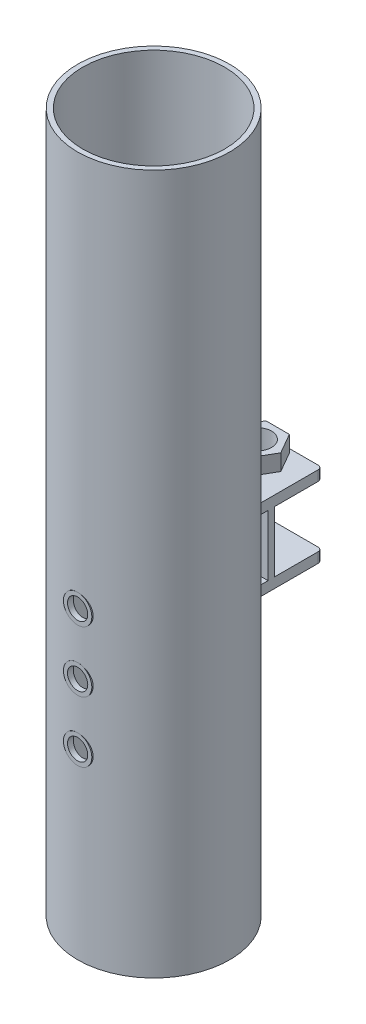
SolidWorks part; units mm, degrees
material "ASTM A36 Steel"
ref_plane "Front Plane" through (0, 0, 0) normal (0, 0, 1) x (1, 0, 0)
ref_plane "Top Plane" through (0, 0, 0) normal (0, 1, 0) x (1, 0, 0)
ref_plane "Right Plane" through (0, 0, 0) normal (1, 0, 0) x (0, 0, -1)
sketch "Sketch1" plane through (0, 0, 0) normal (0, 1, 0) x (1, 0, 0)
  circle A0 centre (0, 0) radius 35
  circle A1 centre (0, 0) radius 37.5
  dimension "D1" = 75
  dimension "D2" = 70
extrude "Boss-Extrude1" add sketch "Sketch1" along normal blind 345
sketch "Sketch2" plane through (0, 0, 0) normal (0, -1, 0) x (1, 0, 0)
  circle A0 centre (0, 0) radius 33.5
  circle A1 centre (0, 0) radius 35.5
  dimension "D1" = 2
extrude "Cut-Extrude1" cut sketch "Sketch2" against normal blind 20
ref_plane "Plane1" through (0, 0, 36.5) normal (0, 0, 1) x (1, 0, 0)
sketch "Sketch3" plane through (0, 0, 36.5) normal (0, 0, 1) x (1, 0, 0)
  line L0 (0, 0) -> (0, 20)
  circle A0 centre (0, 120) radius 5
  circle A1 centre (0, 90) radius 5
  circle A2 centre (0, 150) radius 5
extrude "Cut-Extrude2" cut sketch "Sketch3" against normal blind 30 and the other way blind 10
sketch "Sketch5" plane through (0, 0, 36.5) normal (0, 0, 1) x (1, 0, 0)
  circle A4 centre (0, 120) radius 7
  circle A5 centre (0, 90) radius 7
  circle A6 centre (0, 90) radius 5
  circle A7 centre (0, 120) radius 5
extrude "Boss-Extrude3" add sketch "Sketch5" against normal blind 1 separate body
sketch "Sketch6" plane through (0, 0, 36.5) normal (0, 0, 1) x (1, 0, 0)
  line L0 (0, 90) -> (0, 120)
  line L1 (0, 120) -> (0, 150)
  circle A1 centre (0, 120) radius 7
  circle A4 centre (0, 150) radius 7
  circle A5 centre (0, 120) radius 5
  circle A6 centre (0, 150) radius 5
  circle A8 centre (0, 90) radius 5
  circle A9 centre (0, 90) radius 7
extrude "Boss-Extrude5" add sketch "Sketch6" along normal blind 1
ref_plane "Plane3" through (0, 0, -37.5) normal (0, 0, -1) x (-1, 0, 0)
sketch "Sketch12" plane through (0, 0, -37.5) normal (0, 0, -1) x (-1, 0, 0)
  line L0 (0, 0) -> (0, 130)
  line L1 (0, 130) -> (20, 130)
  line L2 (0, 130) -> (-20, 130)
  line L3 (-20, 130) -> (-20, 135)
  line L4 (-20, 135) -> (20, 135)
  line L5 (20, 135) -> (20, 130)
  line L6 (0, 135) -> (0, 165)
  line L7 (0, 165) -> (-20, 165)
  line L8 (-20, 165) -> (-20, 170)
  line L9 (-20, 170) -> (20, 170)
  line L10 (20, 170) -> (20, 165)
  line L11 (20, 165) -> (0, 165)
extrude "Boss-Extrude7" add sketch "Sketch12" along normal blind 50 and the other way blind 10 separate body contours L11 L10 L9 L8 L7 | L5 L4 L3 L2 L1
sketch "Sketch13" plane through (0, 170, 0) normal (0, 1, 0) x (1, 0, 0)
  line L3 (-20, 63.0803) -> (20, 63.0803)
  line L4 (-20, 27.5) -> (-20, 87.5) construction
  line L5 (20, 27.5) -> (20, 87.5) construction
  line L6 (20, 63.0803) -> (20, 87.5)
  line L7 (20, 87.5) -> (-20, 87.5)
  line L8 (-20, 87.5) -> (-20, 63.0803)
  circle A0 centre (0, 51.134) radius 7
extrude "Cut-Extrude7" cut sketch "Sketch13" against normal blind 21
sketch "Sketch14" plane through (0, 345, 0) normal (0, 1, 0) x (1, 0, 0)
  circle A3 centre (0, 0) radius 35
extrude "Cut-Extrude8" cut sketch "Sketch14" against normal through all
sketch "Sketch15" plane through (0, 170, 0) normal (0, 1, 0) x (1, 0, 0)
  line L1 (11.547, 51.134) -> (5.7735, 61.134)
  line L2 (5.7735, 61.134) -> (-5.7735, 61.134)
  line L3 (-5.7735, 61.134) -> (-11.547, 51.134)
  line L4 (-11.547, 51.134) -> (-5.7735, 41.134)
  line L5 (-5.7735, 41.134) -> (5.7735, 41.134)
  line L6 (5.7735, 41.134) -> (11.547, 51.134)
  circle A0 centre (0, 51.134) radius 7
  circle A2 centre (0, 51.134) radius 10 construction
extrude "Boss-Extrude8" add sketch "Sketch15" along normal blind 8
sketch "Sketch16" plane through (0, 170, 0) normal (0, 1, 0) x (1, 0, 0)
  line L0 (-20, 63.0803) -> (20, 63.0803)
  line L1 (20, 63.0803) -> (20, 87.5)
  line L2 (20, 87.5) -> (-20, 87.5)
  line L3 (-20, 87.5) -> (-20, 63.0803)
extrude "Cut-Extrude11" cut sketch "Sketch16" against normal blind 97
fillet "Fillet1" radius 2 2 edges at (-20, 167.5, -63.0803) (20, 167.5, -63.0803)
fillet "Fillet2" radius 2 2 edges at (-20, 132.5, -63.0803) (20, 132.5, -63.0803)
sketch "Sketch18" plane through (20, 0, 0) normal (1, 0, 0) x (0, 0, -1)
  line L0 (37.4105, 165) -> (36.4159, 165)
  line L1 (28.7228, 165) -> (61.0803, 165) construction
  line L2 (36.4159, 165) -> (36.4159, 135)
  line L3 (28.7228, 135) -> (61.0803, 135) construction
  line L4 (36.4159, 135) -> (39.4901, 135)
  line L5 (39.4901, 135) -> (39.4901, 165)
  line L6 (39.4901, 165) -> (36.4159, 165)
  line M1 (28.7228, 165) -> (61.0803, 165)
extrude "Boss-Extrude12" add sketch "Sketch18" against normal blind 40 contours L4 L5 L2 M1
